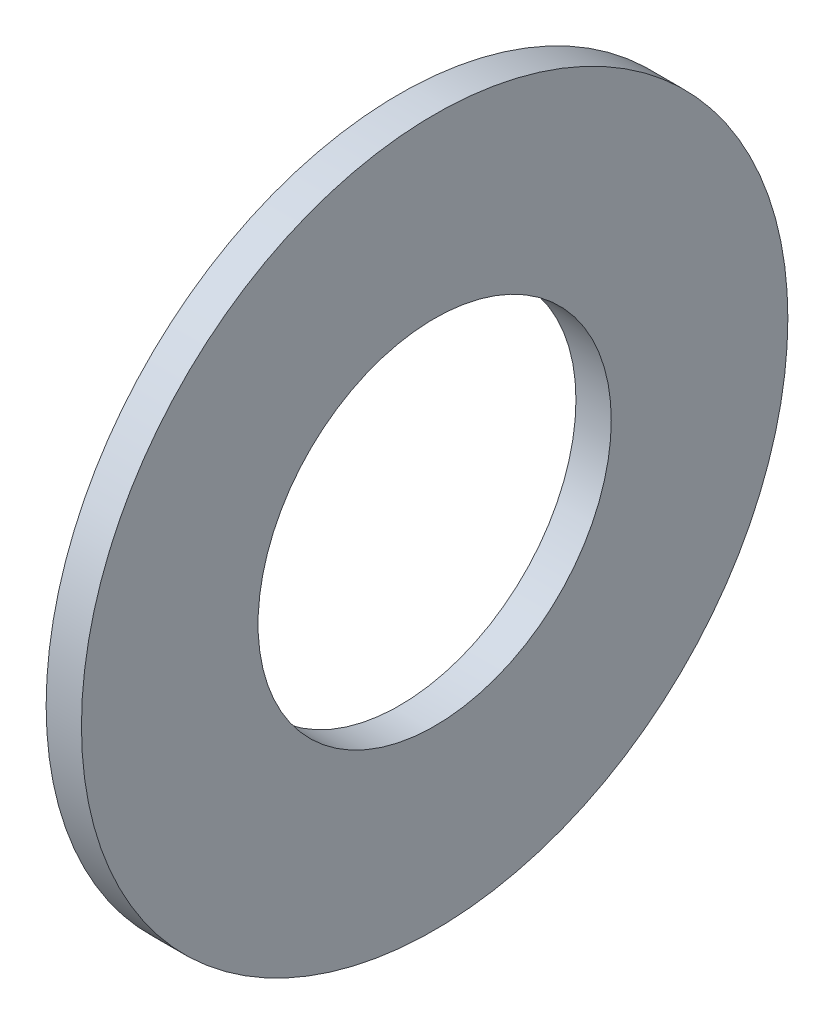
SolidWorks part; units mm, degrees
ref_plane "Front Plane" through (0, 0, 0) normal (0, 0, 1) x (1, 0, 0)
ref_plane "Top Plane" through (0, 0, 0) normal (0, 1, 0) x (1, 0, 0)
ref_plane "Right Plane" through (0, 0, 0) normal (1, 0, 0) x (0, 0, -1)
sketch "Sketch1" plane through (0, 0, 0) normal (1, 0, 0) x (0, 0, -1)
  circle A0 centre (0, 0) radius 2.5
  circle A1 centre (0, 0) radius 5
  dimension "D1" = 5
  dimension "D2" = 10
extrude "Boss-Extrude1" add sketch "Sketch1" along normal blind 0.5
